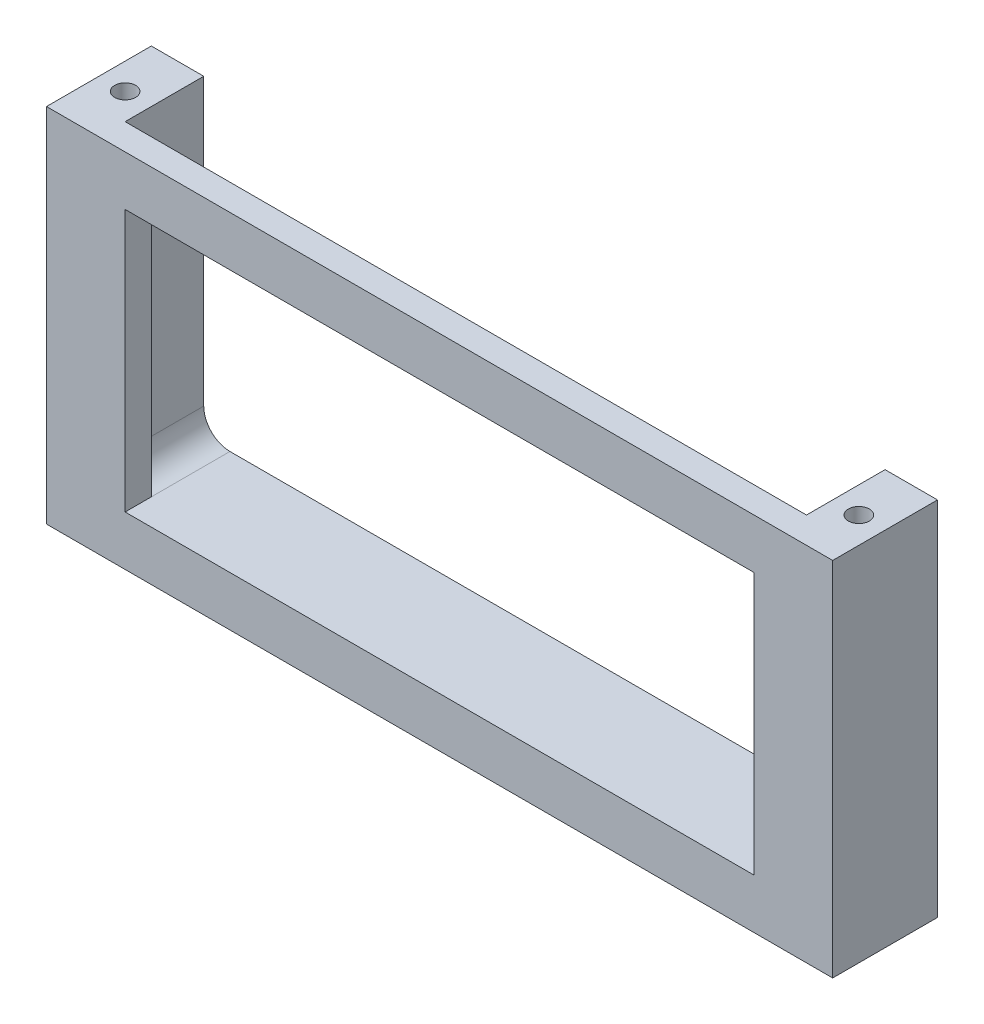
SolidWorks part; units mm, degrees
ref_plane "Front Plane" through (0, 0, 0) normal (0, 0, 1) x (1, 0, 0)
ref_plane "Top Plane" through (0, 0, 0) normal (0, 1, 0) x (1, 0, 0)
ref_plane "Right Plane" through (0, 0, 0) normal (1, 0, 0) x (0, 0, -1)
sketch "Sketch1" plane through (0, 0, 0) normal (0, 1, 0) x (1, 0, 0)
  line L1 (65, 2.5) -> (-65, 2.5)
  line L2 (65, 2.5) -> (65, -2.5)
  line L3 (65, -2.5) -> (-65, -2.5)
  line L4 (-65, 2.5) -> (-65, -2.5)
  line L5 (65, 2.5) -> (-65, -2.5) construction
  line L6 (65, -2.5) -> (-65, 2.5) construction
  point P0 (0, 0)
  dimension "D1" = 130
  dimension "D2" = 5
extrude "Boss-Extrude1" add sketch "Sketch1" along normal blind 69
sketch "Sketch2" plane through (0, 0, 2.5) normal (0, 0, 1) x (1, 0, 0)
  line L0 (-65, 34.5) -> (0, 34.5) construction
  line L5 (-65, 69) -> (-65, 0) construction
  line L6 (0, 34.5) -> (0, 0) construction
  line L7 (-65, 0) -> (65, 0) construction
  line L9 (60, 59.5) -> (-60, 59.5)
  line L10 (60, 59.5) -> (60, 9.5)
  line L11 (60, 9.5) -> (-60, 9.5)
  line L12 (-60, 59.5) -> (-60, 9.5)
  line L13 (60, 59.5) -> (-60, 9.5) construction
  line L14 (60, 9.5) -> (-60, 59.5) construction
  dimension "D1" = 120
  dimension "D2" = 50
extrude "Cut-Extrude1" cut sketch "Sketch2" against normal blind 65
sketch "Sketch3" plane through (0, 0, -2.5) normal (0, 0, -1) x (-1, 0, 0)
  line L0 (75, 0) -> (-75, 0)
  line L1 (-75, 0) -> (-75, 69)
  line L2 (-75, 69) -> (-65, 69)
  line L3 (-65, 69) -> (-65, 9.5)
  line L4 (-65, 9.5) -> (65, 9.5)
  line L5 (65, 9.5) -> (65, 69)
  line L6 (65, 69) -> (75, 69)
  line L7 (75, 69) -> (75, 0)
  line L8 (-65, 69) -> (-65, 0) construction
  line L9 (65, 69) -> (65, 0) construction
  line L10 (60, 9.5) -> (-60, 9.5) construction
  dimension "D1" = 69
  dimension "D3" = 10
extrude "Boss-Extrude3" add sketch "Sketch3" along normal blind 15 and the other way blind 5
sketch "Sketch4" plane through (0, 69, 0) normal (0, 1, 0) x (1, 0, 0)
  line L0 (0, -10.6315) -> (0, 38.8318) construction
  line L1 (-70, 17.5) -> (-70, 7.5) construction
  line L2 (-75, 7.5) -> (75, 7.5) construction
  line L3 (-75, -2.5) -> (-75, 17.5) construction
  line L4 (75, -2.5) -> (75, 17.5) construction
  line L5 (-75, 17.5) -> (-65, 17.5) construction
  circle A0 centre (-70, 7.5) radius 2
  circle A1 centre (70, 7.5) radius 2
  dimension "D1" = 4
extrude "Cut-Extrude2" cut sketch "Sketch4" against normal through all
fillet "Fillet1" radius 5 2 edges at (65, 9.5, -10) (-65, 9.5, -10)
